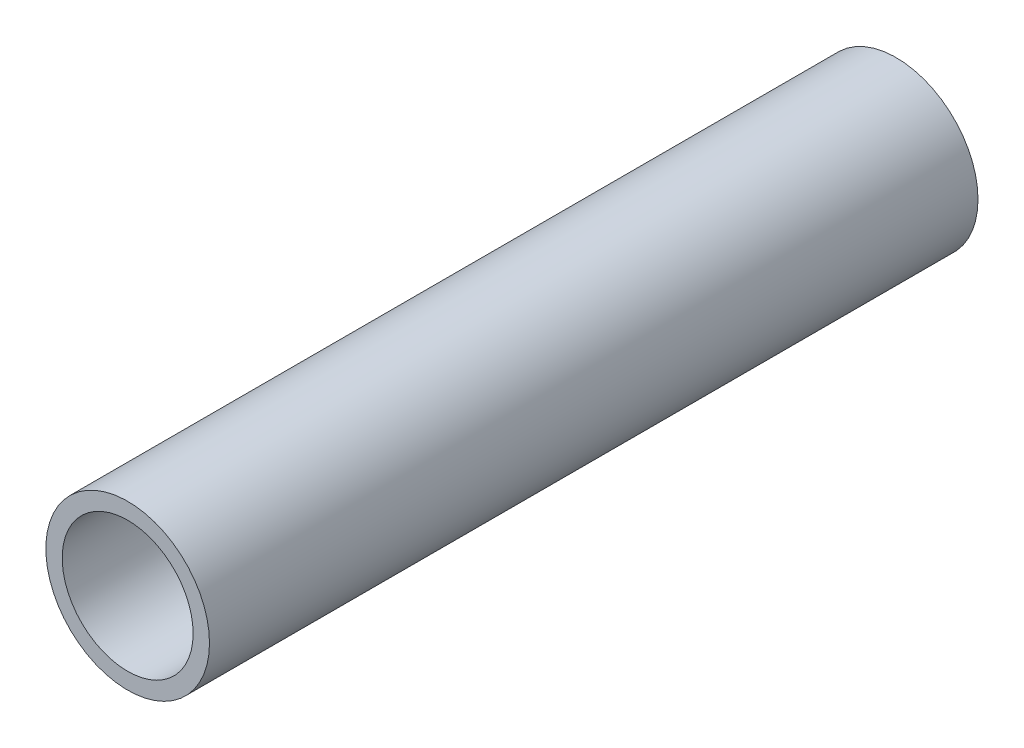
SolidWorks part; units mm, degrees
ref_plane "Front Plane" through (0, 0, 0) normal (0, 0, 1) x (1, 0, 0)
ref_plane "Top Plane" through (0, 0, 0) normal (0, 1, 0) x (1, 0, 0)
ref_plane "Right Plane" through (0, 0, 0) normal (1, 0, 0) x (0, 0, -1)
sketch "Sketch1" plane through (0, 0, 0) normal (0, 0, 1) x (1, 0, 0)
  circle A0 centre (0, 0) radius 1.25
  circle A1 centre (0, 0) radius 1
extrude "Boss-Extrude1" add sketch "Sketch1" along normal blind 11.74
equation "\"D1@Boss-Extrude1\"= \"HL@parametersSketch@prostheticParameters.SLDPRT\" * 0.204 - 4 - 12 - 10'Pinky PIP Tube"
